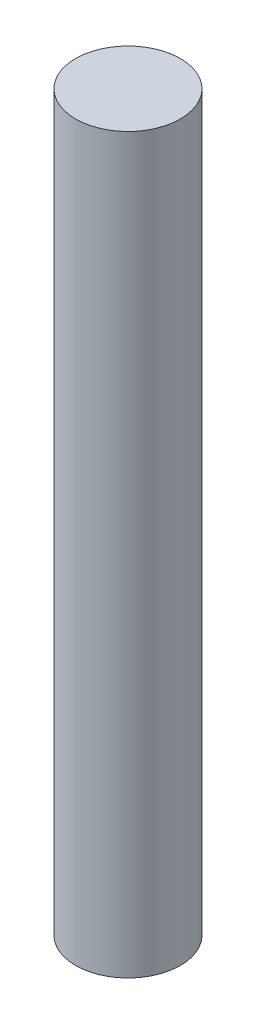
SolidWorks part; units mm, degrees
ref_plane "Front Plane" through (0, 0, 0) normal (0, 0, 1) x (1, 0, 0)
ref_plane "Top Plane" through (0, 0, 0) normal (0, 1, 0) x (1, 0, 0)
ref_plane "Right Plane" through (0, 0, 0) normal (1, 0, 0) x (0, 0, -1)
sketch "Sketch1" plane through (0, 0, 0) normal (0, 1, 0) x (1, 0, 0)
  circle A0 centre (0, 0) radius 1.5875
  dimension "D1" = 3.175
extrude "Boss-Extrude1" add sketch "Sketch1" along normal blind 22.225
